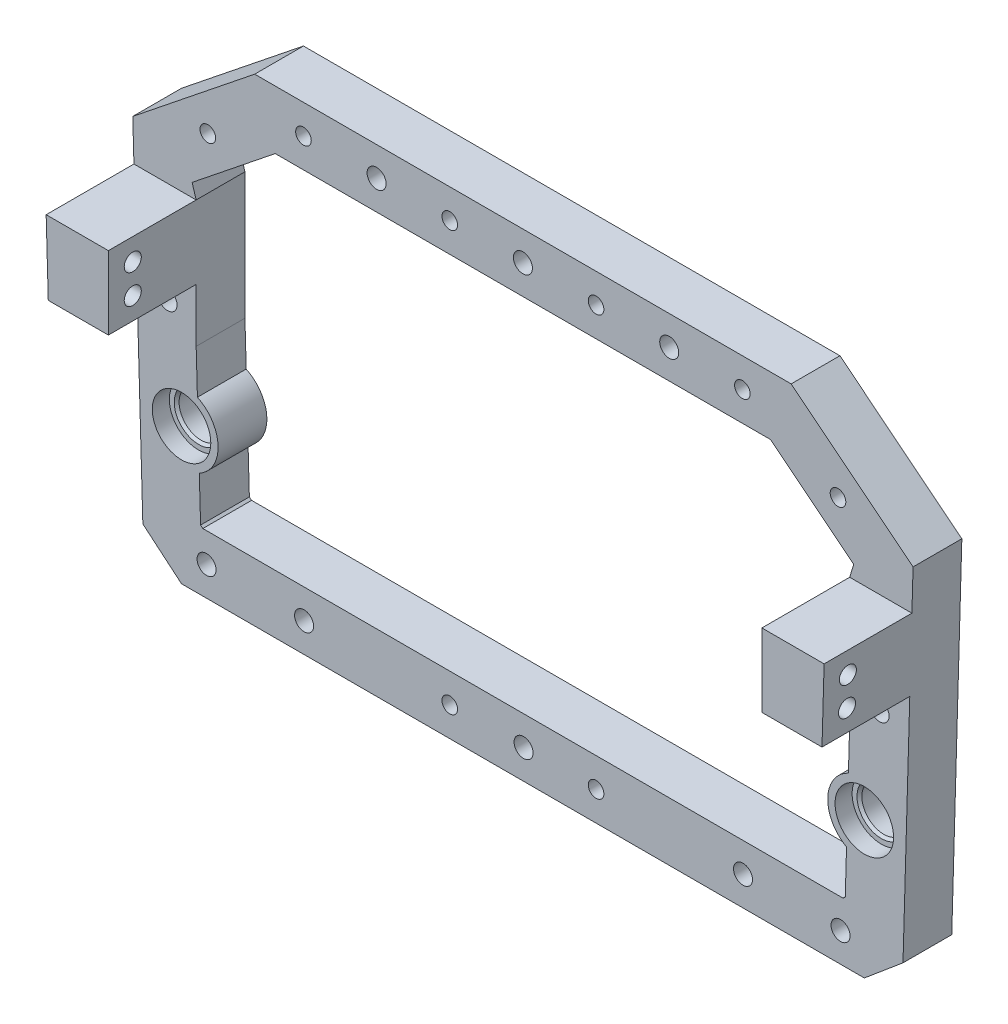
SolidWorks part; units mm, degrees
ref_plane "Ebene vorne" through (0, 0, 0) normal (0, 0, 1) x (1, 0, 0)
ref_plane "Ebene oben" through (0, 0, 0) normal (0, 1, 0) x (1, 0, 0)
ref_plane "Ebene rechts" through (0, 0, 0) normal (1, 0, 0) x (0, 0, -1)
sketch "Sketch1" plane through (0, 0, 0) normal (0, 0, 1) x (1, 0, 0)
  line L0 (-0.1317, -49.025) -> (-0.1317, 48.975) construction
  line L1 (-55.1317, 48.975) -> (54.8683, 48.975)
  line L2 (-70.1317, -49.025) -> (69.8683, -49.025)
  line L3 (-80.1317, 28.975) -> (79.8683, 28.975) construction
  line L4 (-80.1317, 28.975) -> (-55.1317, 48.975)
  line L5 (54.8683, 48.975) -> (79.8683, 28.975)
  line L6 (-70.1317, -49.025) -> (-78.0643, -42.3687)
  line L7 (-80.1317, 28.975) -> (-78.0643, -42.3687)
  line L8 (69.8683, -49.025) -> (77.801, -42.3687)
  line L9 (79.8683, 28.975) -> (77.801, -42.3687)
  line L10 (-78.6828, -21.025) -> (78.4195, -21.025) construction
  line L11 (-67.9634, 23.3421) -> (-50.9223, 36.975)
  line L12 (-50.9223, 36.975) -> (50.6589, 36.975)
  line L13 (50.6589, 36.975) -> (67.7, 23.3421)
  line L15 (65.5007, -37.025) -> (65.962, -36.6379)
  line L16 (-65.764, -37.025) -> (65.5007, -37.025)
  line L17 (-65.764, -37.025) -> (-66.2254, -36.6379)
  line L19 (-66.4878, -27.5803) -> (-66.2254, -36.6379)
  line L20 (66.2245, -27.5803) -> (65.962, -36.6379)
  line L21 (-67.1317, -5.361) -> (66.8683, -5.361) construction
  line L22 (-75.3734, 42.975) -> (77.0259, 42.975) construction
  line L23 (-67.1317, -5.361) -> (-67.1317, 20.639)
  line L24 (-88.185, 14.8487) -> (-38.398, 54.6783) construction
  line L25 (66.8683, -5.361) -> (66.8683, 20.639)
  line L28 (66.8683, -5.361) -> (66.6102, -14.2696)
  line L29 (-67.1317, -5.361) -> (-66.8735, -14.2696)
  line L30 (-67.1317, 20.639) -> (-67.9634, 23.3421)
  line L31 (66.8683, 20.639) -> (67.7, 23.3421)
  line L32 (-88.185, -43.025) -> (105.9173, -43.025) construction
  circle A0 centre (-70.1317, -21.025) radius 6
  circle A1 centre (69.8683, -21.025) radius 6
  arc A2 (-66.4878, -27.5803) -> (-66.8735, -14.2696) centre (-70.1317, -21.025) ccw
  arc A3 (66.6102, -14.2696) -> (66.2245, -27.5803) centre (69.8683, -21.025) ccw
  circle A4 centre (-45.1317, 42.975) radius 1.6
  circle A5 centre (-15.1317, 42.975) radius 1.6
  circle A6 centre (14.8683, 42.975) radius 1.6
  circle A7 centre (44.8683, 42.975) radius 1.6
  circle A8 centre (-64.74, 33.6046) radius 1.6
  circle A9 centre (64.4767, 33.6046) radius 1.6
  circle A10 centre (-15.1317, -43.025) radius 1.6
  circle A11 centre (14.8683, -43.025) radius 1.6
  point P5 (-0.1317, 48.975)
  point P8 (-0.1317, -49.025)
  point P12 (-0.1317, 28.975)
  point P17 (-0.1317, -21.025)
  point P35 (-0.1317, -5.361)
  point P51 (-53.027, 42.975)
  dimension "D10" = 7.5
  dimension "D11" = 12
  dimension "D27" = 134
  dimension "D16" = 3.2
  dimension "D1" = 140
  dimension "D2" = 71.3437
  dimension "D3" = 10.3553
  dimension "D4" = 131.2647
  dimension "D5" = 140
  dimension "D6" = 131.66
  dimension "D7" = 0.6022
  dimension "D8" = 140
  dimension "D9" = 9.0576
  dimension "D12" = 6
  dimension "D13" = 37.6118
  dimension "D14" = 32.0156
  dimension "D15" = 127
  dimension "D17" = 12
  dimension "D18" = 101.5813
  dimension "D19" = 21.8233
  dimension "D20" = 21.8233
  dimension "D21" = 37.6118
  dimension "D22" = 91.66
  dimension "D23" = 140
  dimension "D24" = 131.66
  dimension "D25" = 140
  dimension "D26" = 131.66
  dimension "D28" = 15
  dimension "D29" = 15
  dimension "D30" = 30
  dimension "D31" = 30
  dimension "D32" = 6
  dimension "D33" = 15
  dimension "D34" = 6
  dimension "D35" = 15
  dimension "D36" = 15
extrude "Boss-Extrude1" add sketch "Sketch1" along normal blind 10
sketch "Sketch5" plane through (0, 0, 10) normal (0, 0, 1) x (1, 0, 0)
  line L0 (79.8683, 28.975) -> (77.801, -42.3687) construction
  line L1 (66.8683, 20.639) -> (79.1921, 20.639)
  line L2 (66.8683, 20.639) -> (66.8683, 5.639)
  line L3 (66.8683, 5.639) -> (79.1921, 5.639)
  line L4 (79.1921, 20.639) -> (79.1921, 5.639) construction
  line L5 (79.1921, 20.639) -> (79.6268, 20.639)
  line L6 (79.6268, 20.639) -> (79.1921, 5.639)
  line L7 (-0.1317, 48.975) -> (-0.1317, -49.025) construction
  line L8 (-55.1317, 48.975) -> (54.8683, 48.975) construction
  line L9 (-70.1317, -49.025) -> (69.8683, -49.025) construction
  line L10 (-79.4555, 20.639) -> (-79.4555, 5.639) construction
  line L11 (-79.8901, 20.639) -> (-79.4555, 5.639)
  line L12 (-79.4555, 20.639) -> (-79.8901, 20.639)
  line L13 (-67.1317, 5.639) -> (-79.4555, 5.639)
  line L14 (-67.1317, 20.639) -> (-67.1317, 5.639)
  line L15 (-67.1317, 20.639) -> (-79.4555, 20.639)
  dimension "D1" = 15
extrude "Boss-Extrude2" add sketch "Sketch5" along normal blind 18
sketch "Sketch7" plane through (-67.1317, 0, 0) normal (1, 0, 0) x (0, 0, -1)
  line L0 (-23, 20.639) -> (-23, 5.639) construction
  line L1 (-28, 20.639) -> (-10, 20.639) construction
  line L2 (-28, 5.639) -> (-10, 5.639) construction
  line L3 (-28, 5.639) -> (-28, 20.639) construction
  circle A0 centre (-23, 16.139) radius 1.75
  circle A1 centre (-23, 10.139) radius 1.75
  dimension "D2" = 3.5
  dimension "D3" = 3.5
  dimension "D1" = 5
  dimension "D4" = 4.5
  dimension "D5" = 6
extrude "Cut-Extrude4" cut sketch "Sketch7" against normal through all and the other way through all
sketch "Sketch8" plane through (0, 0, 0) normal (0, 0, -1) x (-1, 0, 0)
  circle A0 centre (-14.8683, 42.975) radius 2.65
  circle A1 centre (15.1317, 42.975) radius 2.65
  circle A2 centre (45.1317, 42.975) radius 2.65
  circle A3 centre (64.74, 33.6046) radius 2.65
  circle A4 centre (-64.4767, 33.6046) radius 2.65
  circle A5 centre (-44.8683, 42.975) radius 2.65
  circle A6 centre (-14.8683, -43.025) radius 2.65
  circle A7 centre (15.1317, -43.025) radius 2.65
  dimension "D1" = 5.3
extrude "Cut-Extrude5" cut sketch "Sketch8" against normal blind 3.5
sketch "Sketch10" plane through (0, 0, 10) normal (0, 0, 1) x (1, 0, 0)
  circle A0 centre (-70.1317, -21.025) radius 4.5
  circle A1 centre (69.8683, -21.025) radius 4.5
  circle A6 centre (-70.1317, -21.025) radius 6.8701
  circle A7 centre (69.8683, -21.025) radius 6.9172
  dimension "D1" = 9
extrude "Boss-Extrude3" add sketch "Sketch10" along normal blind 6.5 from surface at -10 starting at face at (-17.7817, 42.975, 0)
sketch "Sketch11" plane through (0, 0, 0) normal (0, 0, -1) x (-1, 0, 0)
  line L0 (-44.8683, 42.975) -> (45.1317, 42.975) construction
  line L1 (-92.3326, -43.025) -> (95.7716, -43.025) construction
  line L2 (65.764, -37.025) -> (-65.5007, -37.025) construction
  line L3 (79.0287, 0) -> (-79.0287, 0) construction
  line L4 (-79.8683, 28.975) -> (-77.801, -42.3687) construction
  circle A0 centre (-29.8683, 42.975) radius 1.95
  circle A1 centre (0.1317, 42.975) radius 1.95
  circle A2 centre (30.1317, 42.975) radius 1.95
  circle A3 centre (0, -43.025) radius 1.95
  circle A4 centre (-45, -43.025) radius 1.95
  circle A5 centre (45, -43.025) radius 1.95
  circle A6 centre (-65, -43.025) radius 1.95
  circle A7 centre (65, -43.025) radius 1.95
  circle A8 centre (-73, 0) radius 1.95
  circle A9 centre (73, 0) radius 1.95
  point P30 (0, 0)
  dimension "D1" = 3.9
  dimension "D5" = 3.9
  dimension "D8" = 20
  dimension "D2" = 30
  dimension "D3" = 30
  dimension "D4" = 6
  dimension "D6" = 45
  dimension "D7" = 45
  dimension "D9" = 20
  dimension "D10" = 73
  dimension "D11" = 73
extrude "Cut-Extrude6" cut sketch "Sketch11" against normal through all
chamfer "Chamfer1" distance 0.5 angle 45 2 edges at (-65.6317, -21.025, 6.5) (74.3683, -21.025, 6.5)
